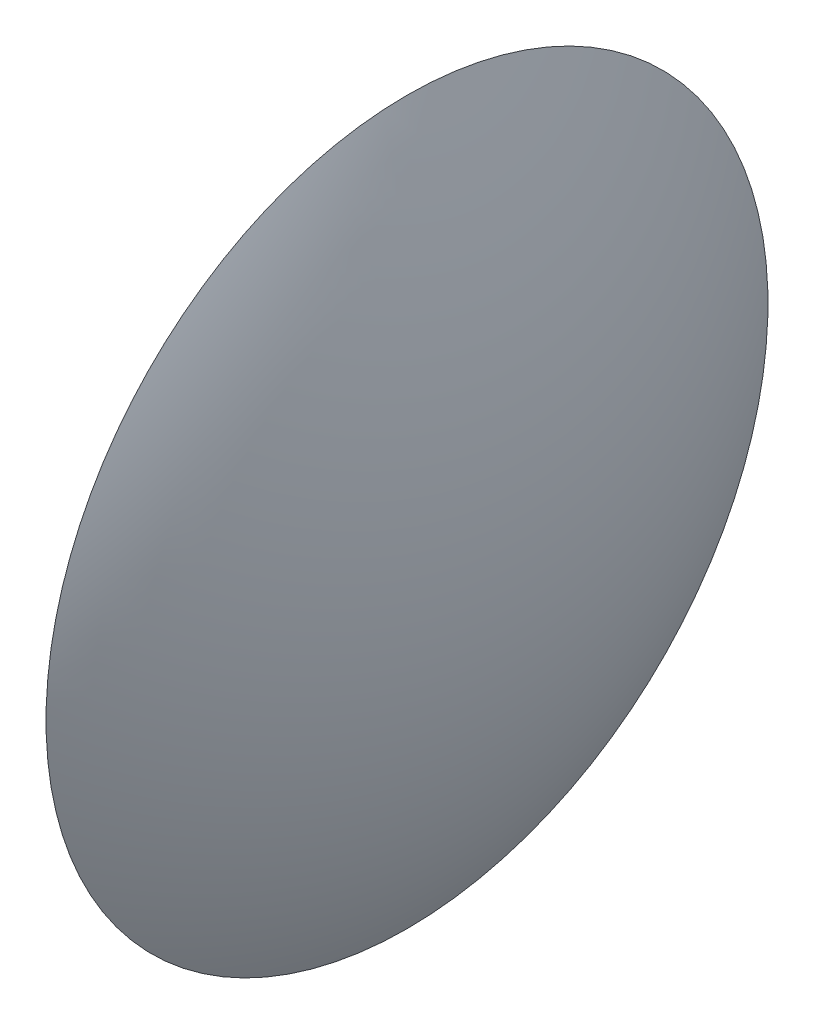
SolidWorks part; units mm, degrees
ref_plane "Front Plane" through (0, 0, 0) normal (0, 0, 1) x (1, 0, 0)
ref_plane "Top Plane" through (0, 0, 0) normal (0, 1, 0) x (1, 0, 0)
ref_plane "Right Plane" through (0, 0, 0) normal (1, 0, 0) x (0, 0, -1)
sketch "Sketch1" plane through (0, 0, 0) normal (0, 0, 1) x (1, 0, 0)
  line L0 (0.5, 0) -> (-0.5, 0)
  line L1 (-0.5, 0) -> (-0.5, 3.9)
  line L2 (-2.4505, 0) -> (1.9498, 0) construction
  arc A0 (0.5, 0) -> (-0.5, 3.9) centre (-7.605, 0) ccw
  dimension "D1" = 3.9
  dimension "D2" = 1
  dimension "D3" = 0.5
revolve "Revolve1" add sketch "Sketch1" angle 360 about L2
